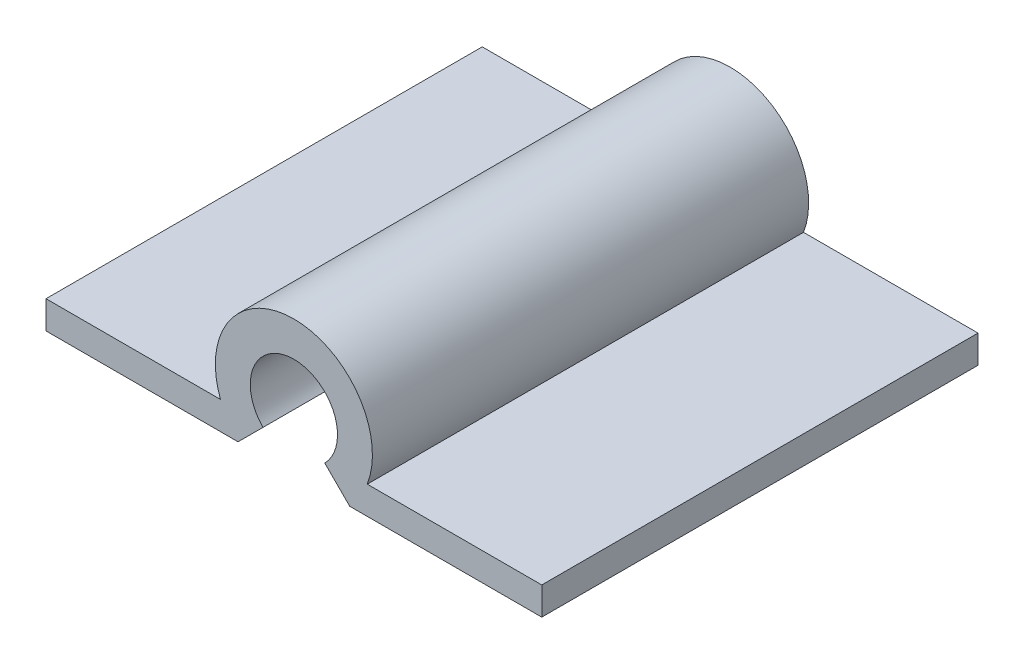
SolidWorks part; units mm, degrees
ref_plane "Front Plane" through (0, 0, 0) normal (0, 0, 1) x (1, 0, 0)
ref_plane "Top Plane" through (0, 0, 0) normal (0, 1, 0) x (1, 0, 0)
ref_plane "Right Plane" through (0, 0, 0) normal (1, 0, 0) x (0, 0, -1)
sketch "Sketch1" plane through (0, 0, 0) normal (0, 0, 1) x (1, 0, 0)
  line L0 (-2.6708, -1.016) -> (-9.0208, -1.016)
  line L1 (2.6708, -1.016) -> (9.0208, -1.016)
  line L2 (-9.0208, -2.032) -> (-2.032, -2.032)
  line L3 (2.032, -2.032) -> (9.0208, -2.032)
  line L4 (2.032, -2.032) -> (1.1225, -1.1225)
  line L5 (-2.032, -2.032) -> (-1.1225, -1.1225)
  line L6 (-9.0208, -1.016) -> (-9.0208, -2.032)
  line L7 (9.0208, -1.016) -> (9.0208, -2.032)
  arc A0 (1.1225, -1.1225) -> (-1.1225, -1.1225) centre (0, 0) ccw
  arc A1 (2.6708, -1.016) -> (-2.6708, -1.016) centre (0, 0) ccw
  circle A2 centre (0, 0) radius 2.8575 construction
  circle A3 centre (0, 0) radius 1.5875 construction
  point P4 (-5.5264, -2.032)
  dimension "D1" = 3.175
  dimension "D3" = 6.35
  dimension "D4" = 1.016
  dimension "D5" = 1.016
  dimension "D6" = 135
  dimension "D7" = 135
  dimension "D2" = 1.27
extrude "Boss-Extrude1" add sketch "Sketch1" along normal blind 15.875 contours L0 L6 L2 L5 A0 L4 L3 L7 L1 A1
